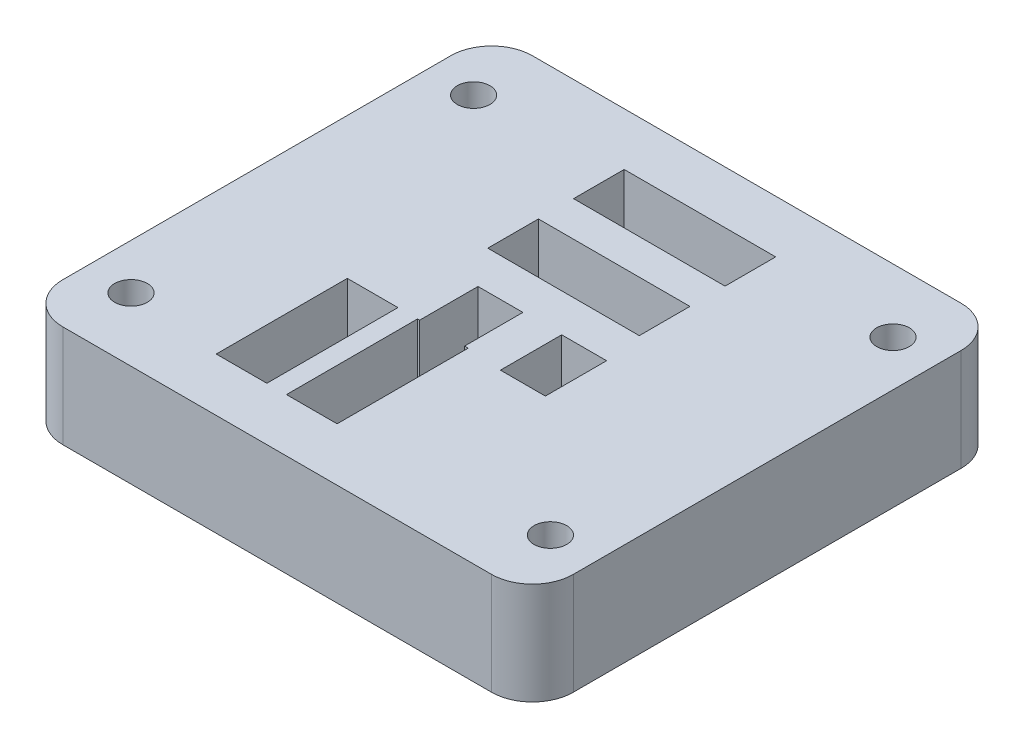
SolidWorks part; units mm, degrees
ref_plane "Front Plane" through (0, 0, 0) normal (0, 0, 1) x (1, 0, 0)
ref_plane "Top Plane" through (0, 0, 0) normal (0, 1, 0) x (1, 0, 0)
ref_plane "Right Plane" through (0, 0, 0) normal (1, 0, 0) x (0, 0, -1)
sketch "Sketch3" plane through (0, 0, 0) normal (0, 1, 0) x (1, 0, 0)
  line L0 (0, 0) -> (0, 35.7675) construction
  line L1 (0, 0) -> (-48.2343, 0) construction
  line L3 (-15.875, 14.605) -> (15.875, 14.605)
  line L4 (-15.875, 14.605) -> (-15.875, -14.605)
  line L5 (-15.875, -14.605) -> (15.875, -14.605)
  line L6 (15.875, 14.605) -> (15.875, -14.605)
  point P0 (0, 14.605)
  point P1 (-15.875, 0)
  dimension "D1" = 0
  dimension "D4" = 0
  dimension "D2" = 31.75
  dimension "D3" = 29.21
extrude "Boss-Extrude2" add sketch "Sketch3" along normal blind 6.35
sketch "Sketch1" plane through (0, 0, 0) normal (0, 1, 0) x (1, 0, 0)
  line L0 (11.9677, 5.588) -> (11.9677, -5.588)
  line L1 (0, 0) -> (0, 78.5916) construction
  line L2 (0, 0) -> (-90.5086, 0) construction
  arc A1 (11.9677, 5.588) -> (11.9677, -5.588) centre (0, 0) ccw
  dimension "D1" = 11.176
  dimension "D2" = 13.208
  dimension "D3" = 0
  dimension "D4" = 0
extrude "Cut-Extrude1" cut sketch "Sketch1" along normal blind 0.8636
sketch "Sketch6" plane through (0, 6.35, 0) normal (0, 1, 0) x (1, 0, 0)
  line L0 (0, 0) -> (0, 10.2024) construction
  line L1 (0, 0) -> (-12.8679, 0) construction
  circle A0 centre (-13.0429, 10.6553) radius 1.016
  circle A1 centre (13.0429, 10.6553) radius 1.016
  circle A2 centre (13.0429, -10.6553) radius 1.016
  circle A3 centre (-13.0429, -10.6553) radius 1.016
  dimension "D1" = 10.6553
  dimension "D3" = 2.032
  dimension "D2" = 13.0429
extrude "Cut-Extrude3" cut sketch "Sketch6" against normal blind 8.89
sketch "Sketch4" plane through (0, 0.8636, 0) normal (0, -1, 0) x (1, 0, 0)
  line L0 (-36.8277, 0) -> (36.8277, 0) construction
  line L5 (-4.3561, -8.1841) -> (5.0673, -8.1841)
  line L6 (-4.3561, -8.1841) -> (-4.3561, -11.3337)
  line L7 (-4.3561, -11.3337) -> (5.0673, -11.3337)
  line L8 (5.0673, -8.1841) -> (5.0673, -11.3337)
  line L13 (-7.0993, 11.2977) -> (-3.9497, 11.2977)
  line L14 (-7.0993, 11.2977) -> (-7.0993, 3.1443)
  line L15 (-7.0993, 3.1443) -> (-3.9497, 3.1443)
  line L16 (-3.9497, 11.2977) -> (-3.9497, 3.1443)
  line L17 (0, 36.8277) -> (0, -36.8277) construction
  line L18 (-4.3561, -2.8501) -> (5.0673, -2.8501)
  line L19 (5.0673, -2.8501) -> (5.0673, -5.9997)
  line L20 (-4.3561, -5.9997) -> (5.0673, -5.9997)
  line L21 (-4.3561, -2.8501) -> (-4.3561, -5.9997)
  line L22 (-2.7305, 11.2977) -> (0.4191, 11.2977)
  line L23 (-2.7305, 11.2977) -> (-2.7305, 3.1443)
  line L24 (-2.7305, 3.1443) -> (0.4191, 3.1443)
  line L25 (0.4191, 11.2977) -> (0.4191, 3.1443)
  line L26 (-13.0429, 10.6553) -> (-13.0429, -18.3804) construction
  line L27 (-13.0429, -10.6733) -> (15.8538, -10.6733) construction
  dimension "D2" = 8.6868
  dimension "D1" = 9.4234
  dimension "D3" = 3.1496
  dimension "D4" = 0.6604
  dimension "D5" = 2
  dimension "D6" = 13.8176
  dimension "D7" = 2.1844
  dimension "D8" = 3.1496
  dimension "D9" = 5.9436
  dimension "D10" = 8.1534
  dimension "D11" = 2
  dimension "D12" = 1.2192
extrude "Cut-Extrude2" cut sketch "Sketch4" against normal through all
sketch "Sketch7" plane through (0, 0.8636, 0) normal (0, -1, 0) x (1, 0, 0)
  line L0 (11.8796, 4.9907) -> (11.8796, 27.6879) construction
  line L19 (0, 0) -> (-32.9753, 0) construction
  line L20 (-2.5984, 3.3274) -> (0.1956, 3.3274)
  line L21 (-2.5984, 3.3274) -> (-2.5984, -0.4826)
  line L22 (-2.5984, -0.4826) -> (0.1956, -0.4826)
  line L23 (0.1956, 3.3274) -> (0.1956, -0.4826)
  line L28 (2.6086, 3.3274) -> (2.6086, -0.4826)
  line L29 (2.6086, 3.3274) -> (5.4026, 3.3274)
  line L30 (5.4026, 3.3274) -> (5.4026, -0.4826)
  line L31 (2.6086, -0.4826) -> (5.4026, -0.4826)
  dimension "D1" = 14.478
  dimension "D2" = 0.4826
  dimension "D3" = 2.794
  dimension "D4" = 3.81
  dimension "D6" = 2.413
  dimension "D5" = 2
extrude "Cut-Extrude4" cut sketch "Sketch7" against normal through all
fillet "Fillet1" radius 2.54 4 edges at (-15.875, 3.175, -14.605) (-15.875, 3.175, 14.605) (15.875, 3.175, 14.605) (15.875, 3.175, -14.605)
sketch "Sketch9" plane through (0, 0.8636, 0) normal (0, -1, 0) x (1, 0, 0)
  line L0 (-200036.8277, 0) -> (200036.8277, 0) construction
  line L1 (-13.208, 0) -> (-13.208, -22.717) construction
  line L2 (-21.9767, 0) -> (29.9324, 0) construction
  circle A0 centre (8.7503, 3.7592) radius 0.4445
  circle A1 centre (8.7503, -3.7592) radius 0.4445
  dimension "D2" = 0.889
  dimension "D1" = 3.7592
  dimension "D3" = 21.9583
extrude "Boss-Extrude3" add sketch "Sketch9" along normal blind 0.8128
fillet "Fillet2" radius 0.254 2 edges at (8.7503, 0.0508, -3.3147) (8.7503, 0.0508, 3.3147)
